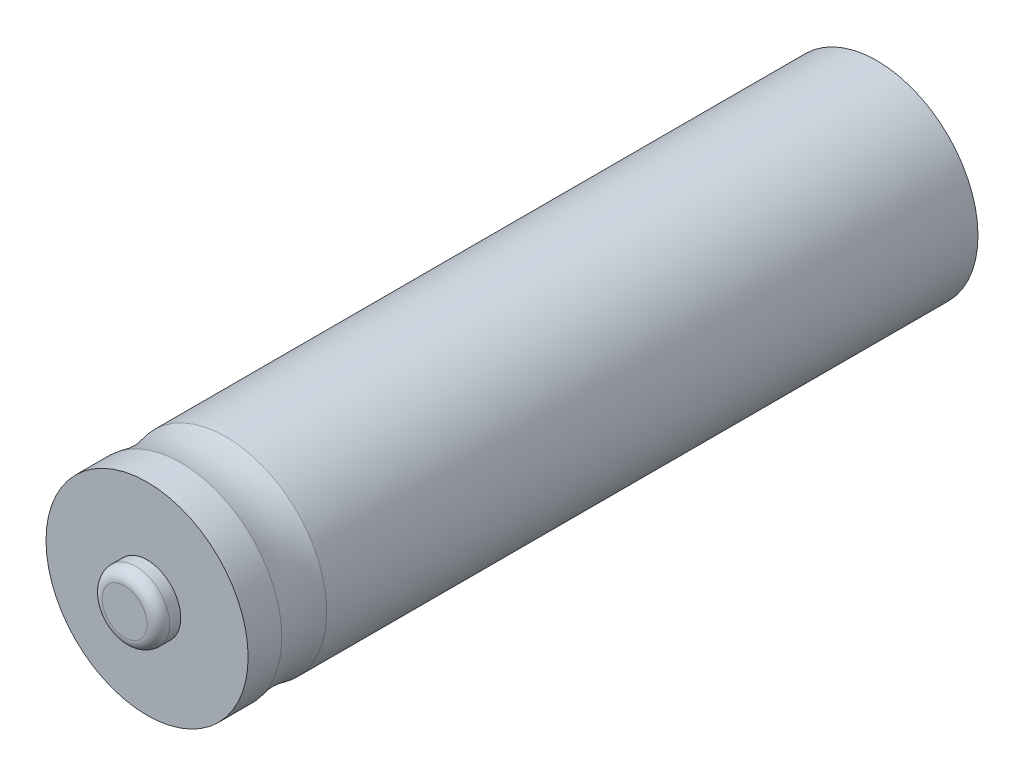
SolidWorks part; units mm, degrees
ref_plane "Plano frontal" through (0, 0, 0) normal (0, 0, 1) x (1, 0, 0)
ref_plane "Plano superior" through (0, 0, 0) normal (0, 1, 0) x (1, 0, 0)
ref_plane "Plano direito" through (0, 0, 0) normal (1, 0, 0) x (0, 0, -1)
sketch "Esboço1" plane through (0, 0, 0) normal (0, 0, 1) x (1, 0, 0)
  circle A0 centre (0, 0) radius 9
  dimension "D1" = 18
extrude "Ressalto-extrusão1" add sketch "Esboço1" along normal mid plane 65
sketch "Esboço2" plane through (0, 0, 32.5) normal (0, 0, 1) x (1, 0, 0)
  circle A0 centre (0, 0) radius 3
  dimension "D1" = 6
extrude "Ressalto-extrusão2" add sketch "Esboço2" along normal blind 2
fillet "Filete1" radius 1 1 edges at (3, 0, 34.5)
sketch "Esboço3" plane through (0, 0, 0) normal (1, 0, 0) x (0, 0, -1)
  line L4 (-34.5, 0) -> (-40.2176, 0) construction
  line L5 (-34.5, 2) -> (-34.5, -2) construction
  line L6 (-29.5, 9) -> (-25.5, 9)
  arc A0 (-29.5, 9) -> (-25.5, 9) centre (-27.5, 16.5444) ccw
revolve "Corte-Revolução1" cut sketch "Esboço3" angle 360 about L4
sketch "Esboço4" plane through (0, 0, -32.5) normal (0, 0, -1) x (-1, 0, 0)
  circle A0 centre (0, 0) radius 5.5
  dimension "D1" = 11
extrude "Ressalto-extrusão3" add sketch "Esboço4" along normal blind 0.4
